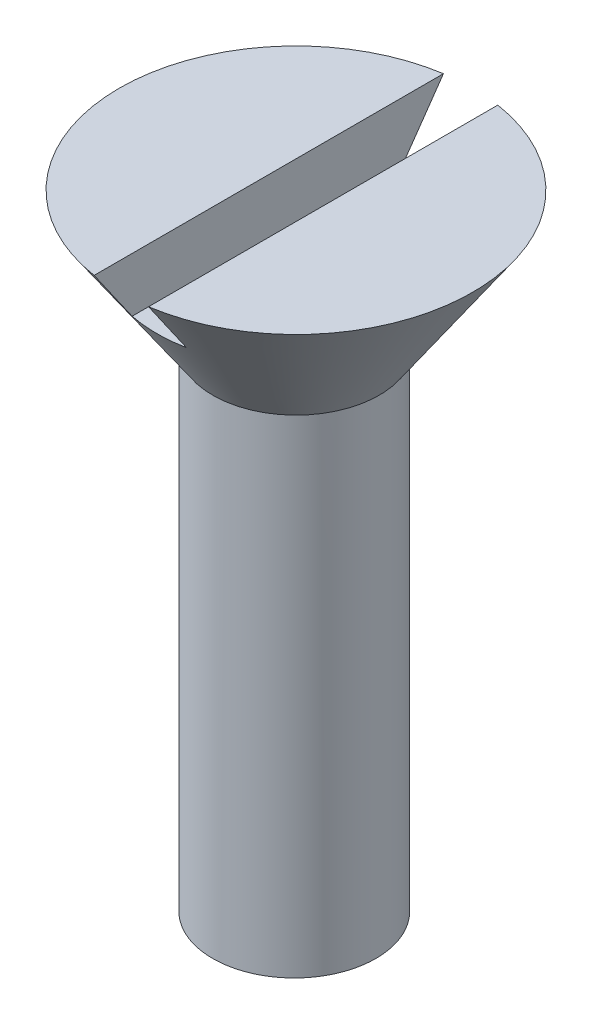
SolidWorks part; units mm, degrees
ref_plane "Front Plane" through (0, 0, 0) normal (0, 0, 1) x (1, 0, 0)
ref_plane "Top Plane" through (0, 0, 0) normal (0, 1, 0) x (1, 0, 0)
ref_plane "Right Plane" through (0, 0, 0) normal (1, 0, 0) x (0, 0, -1)
sketch "Sketch1" plane through (0, 0, 0) normal (0, 0, 1) x (1, 0, 0)
  line L0 (-0.0622, 9) -> (-0.0622, -9) construction
  line L1 (-3.0622, 9) -> (-0.0622, 9)
  line L2 (-3.0622, 9) -> (-3.0622, -9)
  line L3 (-3.0622, -9) -> (-0.0622, -9)
  line L5 (-0.0622, 9) -> (-0.0622, -9)
  point P0 (0, 0)
  dimension "D1" = 18
  dimension "D2" = 3
revolve "Revolve2" add sketch "Sketch1" angle 360 about L0
sketch "Sketch3" plane through (0, 0, 0) normal (0, 0, 1) x (1, 0, 0)
  line L0 (3.0622, 9) -> (0, 9)
  line L1 (0, 14) -> (6.5, 14)
  line L2 (0, 14) -> (0, 9)
  line L3 (2.9378, 9) -> (-3.0622, 9) construction
  line L5 (3.0622, 9) -> (6.5, 14)
revolve "Revolve3" add sketch "Sketch3" angle 360 about L2
sketch "Sketch4" plane through (0, 0, 0) normal (0, 0, 1) x (1, 0, 0)
  line L0 (1, 14) -> (1, 12)
  line L1 (6.5, 14) -> (-6.5, 14) construction
  line L2 (1, 12) -> (-1, 12)
  line L3 (-1, 12) -> (-1, 14)
  point P4 (0, 12)
  point P8 (0, 0)
  point P10 (0, 0)
  dimension "D1" = 6.5
  dimension "D2" = 2
  dimension "D3" = 2
extrude "Cut-Extrude1" cut sketch "Sketch4" against normal through all and the other way through all flip side to cut
sketch "Sketch5" plane through (0, 0, 0) normal (0, 0, 1) x (1, 0, 0)
  line L0 (2.9378, -9) -> (0, -10.6961)
  line L1 (0, -10.6961) -> (0, -9)
  line L2 (0, -9) -> (2.9378, -9)
  dimension "D1" = 60
revolve "Revolve4" add sketch "Sketch5" angle 360 about L1
